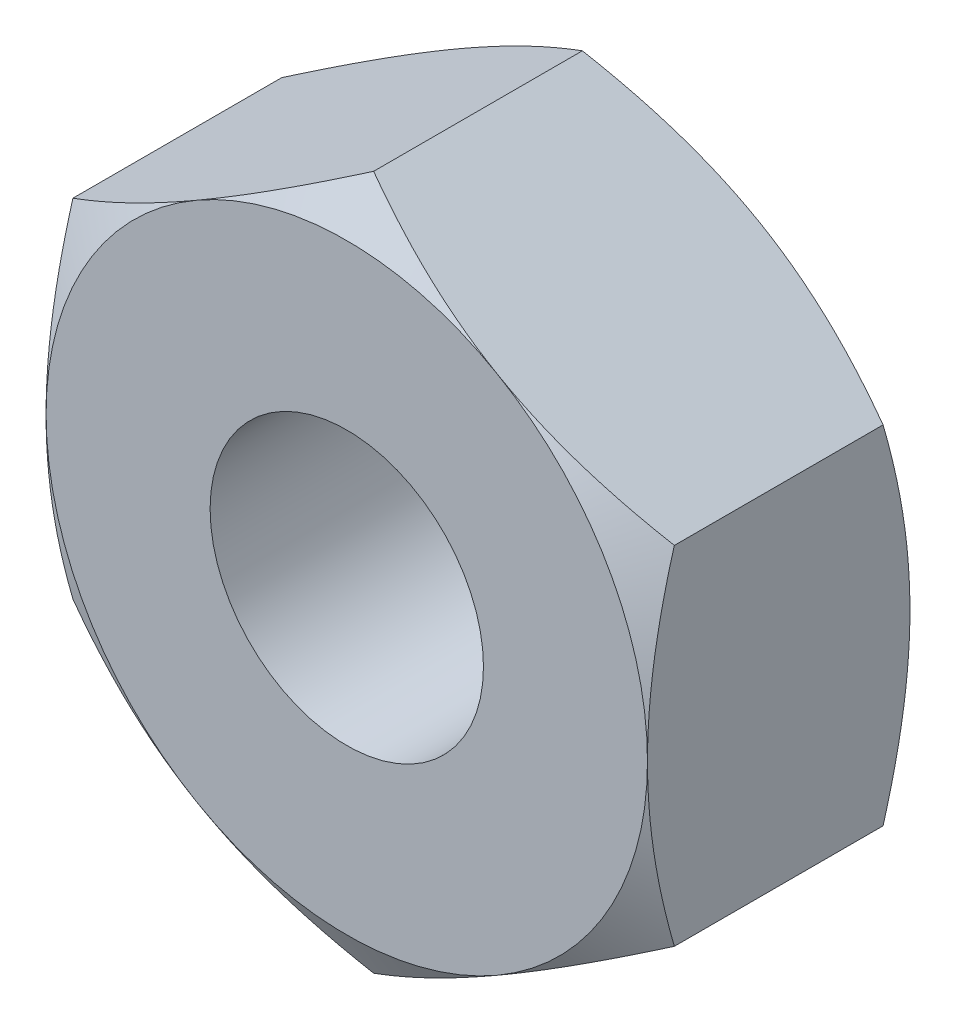
SolidWorks part; units mm, degrees
material "Plain Carbon Steel"
ref_plane "Front Plane" through (0, 0, 0) normal (0, 0, 1) x (1, 0, 0)
ref_plane "Top Plane" through (0, 0, 0) normal (0, 1, 0) x (1, 0, 0)
ref_plane "Right Plane" through (0, 0, 0) normal (1, 0, 0) x (0, 0, -1)
sketch "Sketch2" plane through (0, 0, 0) normal (0, 0, 1) x (1, 0, 0)
  line L0 (2.75, 1.5877) -> (2.75, -1.5877)
  line L1 (-2.75, 1.5877) -> (-2.75, -1.5877)
  line L2 (2.75, 1.5877) -> (0, 3.1754)
  line L3 (0, 3.1754) -> (-2.75, 1.5877)
  line L4 (-2.75, -1.5877) -> (0, -3.1754)
  line L5 (0, -3.1754) -> (2.75, -1.5877)
  circle A0 centre (0, 0) radius 1.25
  dimension "D3" = 2.5
  dimension "D1" = 5.5
  dimension "D2" = 120
  dimension "D4" = 2.75
extrude "Boss-Extrude1" add sketch "Sketch2" along normal mid plane 2.4
sketch "Sketch3" plane through (0, 0, -1.2) normal (0, 0, -1) x (-1, 0, 0)
  line L0 (0, 3.1754) -> (2.75, 1.5877) construction
  line L1 (-2.75, 1.5877) -> (0, 3.1754) construction
  line L2 (-2.75, 1.5877) -> (-2.75, -1.5877) construction
  line L3 (0, -3.1754) -> (-2.75, -1.5877) construction
  line L4 (2.75, -1.5877) -> (0, -3.1754) construction
  line L5 (2.75, 1.5877) -> (2.75, -1.5877) construction
  line L6 (0, 3.1754) -> (2.75, 1.5877) construction
  line L7 (-2.75, 1.5877) -> (0, 3.1754) construction
  line L8 (-2.75, 1.5877) -> (-2.75, -1.5877) construction
  line L9 (0, -3.1754) -> (-2.75, -1.5877) construction
  line L10 (2.75, -1.5877) -> (0, -3.1754) construction
  line L11 (2.75, 1.5877) -> (2.75, -1.5877) construction
  circle A0 centre (0, 0) radius 2.75 construction
sketch "Sketch4" plane through (0, 0, 0) normal (1, 0, 0) x (0, 0, -1)
  line L0 (1.2, -2.75) -> (1.2, 2.75) construction
  line L1 (1.2, -2.75) -> (1.2, 2.75) construction
  line L2 (1.2, 2.75) -> (1.2, 4.3287)
  line L3 (1.2, 4.3287) -> (0.2886, 4.3287)
  line L4 (0.2886, 4.3287) -> (1.2, 2.75)
  line L6 (-2.9945, 0) -> (4.4636, 0) construction
  dimension "D1" = 30
revolve "Cut-Revolve2" cut sketch "Sketch4" angle 360 about L6
mirror "Mirror1" about plane through (0, 0, 0) normal (0, 0, 1) of "Cut-Revolve2"
